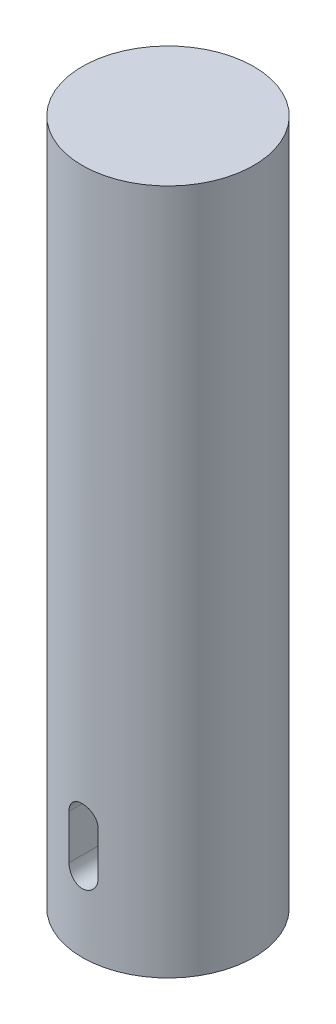
SolidWorks part; units mm, degrees
ref_plane "Vorne" through (0, 0, 0) normal (0, 0, 1) x (1, 0, 0)
ref_plane "Oben" through (0, 0, 0) normal (0, 1, 0) x (1, 0, 0)
ref_plane "Rechts" through (0, 0, 0) normal (1, 0, 0) x (0, 0, -1)
sketch "Skizze1" plane through (0, 0, 0) normal (0, 1, 0) x (1, 0, 0)
  circle A0 centre (0, 0) radius 25
  dimension "D1" = 50
extrude "Aufsatz-Linear austragen1" add sketch "Skizze1" along normal blind 200
ref_plane "Ebene1" through (0, 0, 25) normal (0, 0, 1) x (1, 0, 0)
sketch "Skizze2" plane through (0, 0, 25) normal (0, 0, 1) x (1, 0, 0)
  line L0 (0, 21.6412) -> (0, 34.628) construction
  line L1 (-4.2348, 21.6412) -> (-4.2348, 34.628)
  line L2 (4.2348, 21.6412) -> (4.2348, 34.628)
  arc A0 (-4.2348, 21.6412) -> (4.2348, 21.6412) centre (0, 21.6412) ccw
  arc A1 (4.2348, 34.628) -> (-4.2348, 34.628) centre (0, 34.628) ccw
  point P3 (0, 28.1346)
extrude "Schnitt-Linear austragen1" cut sketch "Skizze2" against normal blind 10
